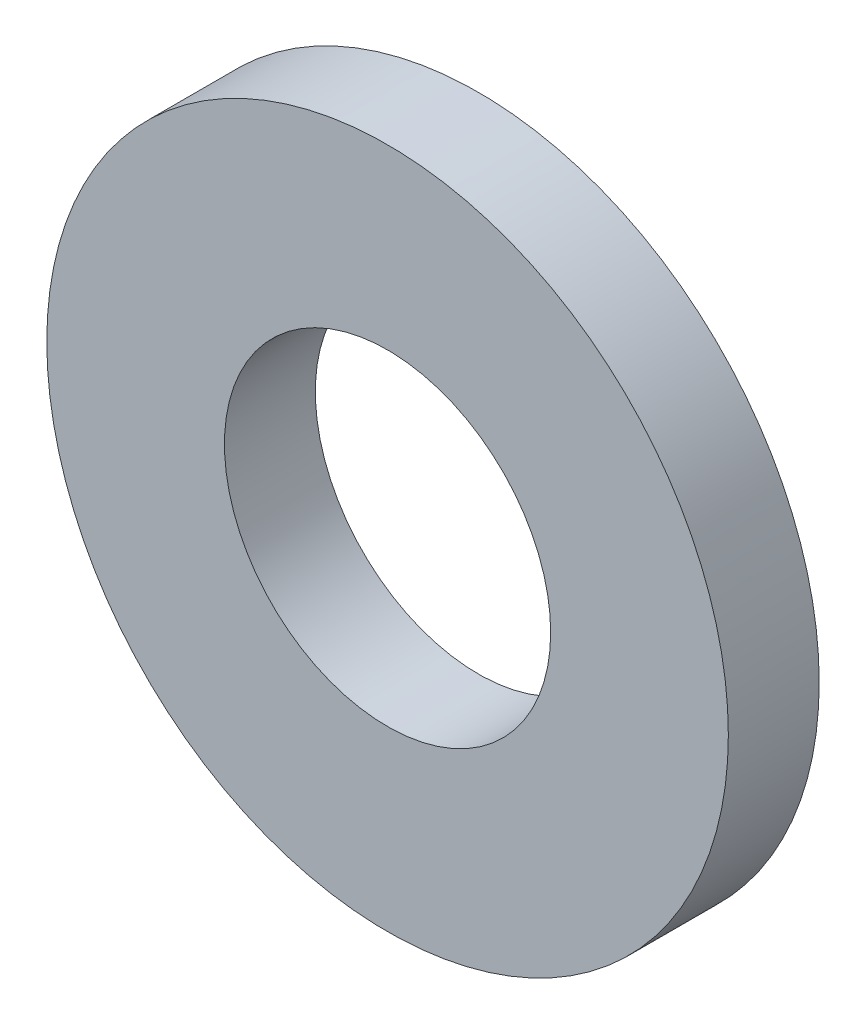
SolidWorks part; units mm, degrees
ref_plane "Plan de face" through (0, 0, 0) normal (0, 0, 1) x (1, 0, 0)
ref_plane "Plan de dessus" through (0, 0, 0) normal (0, 1, 0) x (1, 0, 0)
ref_plane "Plan de droite" through (0, 0, 0) normal (1, 0, 0) x (0, 0, -1)
sketch "Esquisse1" plane through (0, 0, 0) normal (0, 0, 1) x (1, 0, 0)
  circle A0 centre (0, 0) radius 3.59
  circle A1 centre (0, 0) radius 7.5
  dimension "D1" = 7.18
  dimension "D2" = 15
extrude "Boss.-Extru.1" add sketch "Esquisse1" along normal blind 2
